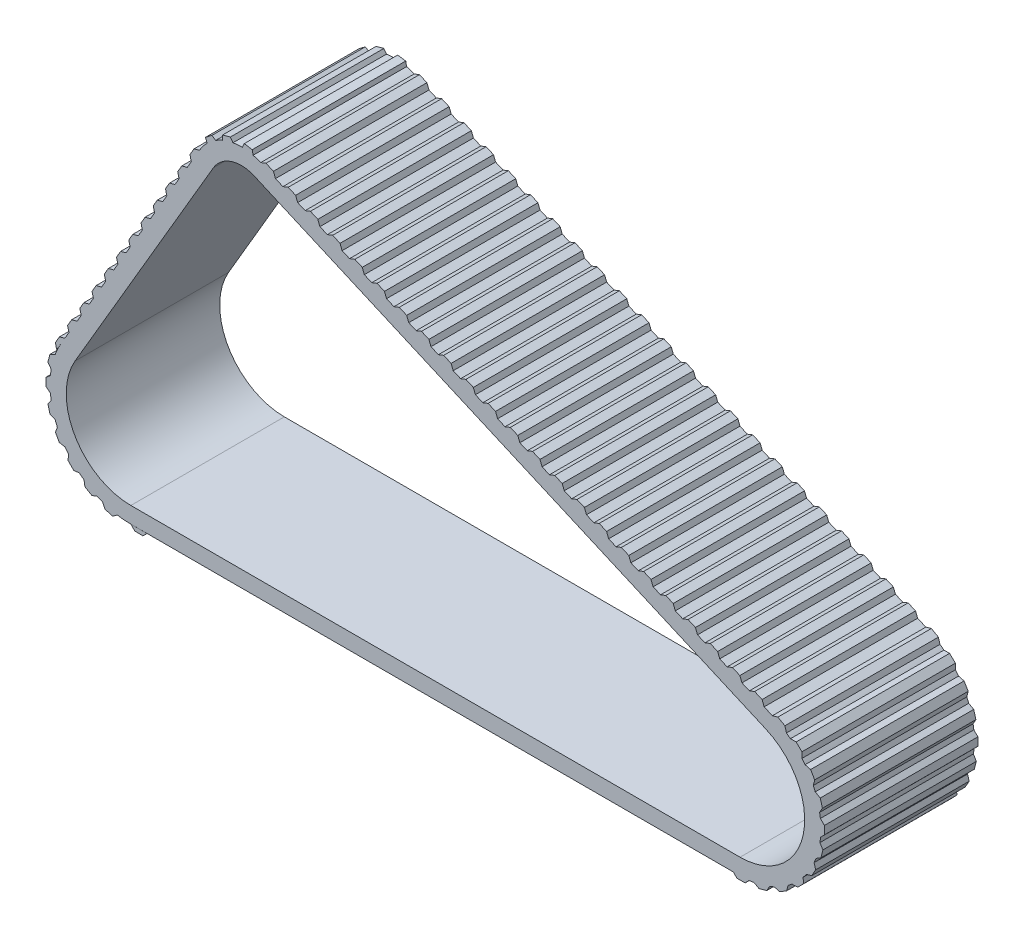
SolidWorks part; units mm, degrees
material "Caucho"
ref_plane "Alzado" through (0, 0, 0) normal (0, 0, 1) x (1, 0, 0)
ref_plane "Planta" through (0, 0, 0) normal (0, 1, 0) x (1, 0, 0)
ref_plane "Vista lateral" through (0, 0, 0) normal (1, 0, 0) x (0, 0, -1)
sketch "Croquis1" plane through (0, 0, 0) normal (0, 0, 1) x (1, 0, 0)
  line L0 (8.4952, 34.325) -> (-8.6315, 5.0496)
  line L1 (16.0728, 36.7949) -> (79.4167, 9.166)
  line L2 (0, -10) -> (75.4188, -10)
  arc A0 (-8.6315, 5.0496) -> (0, -10) centre (0, 0) ccw
  arc A1 (75.4188, -10) -> (79.4167, 9.166) centre (75.4188, 0) ccw
  arc A2 (16.0728, 36.7949) -> (8.4952, 34.325) centre (13.6741, 31.2953) ccw
extrude "Extruir1" add sketch "Croquis1" along normal blind 19
shell "Vaciado1" thickness 2
sketch "Croquis2" plane through (0, 0, 2) normal (0, 0, 1) x (1, 0, 0)
  line L0 (10.2215, 33.3151) -> (-6.9052, 4.0396)
  line L1 (0, -8) -> (75.4188, -8)
  line L2 (78.6171, 7.3328) -> (15.2732, 34.9617)
  arc A0 (15.2732, 34.9617) -> (10.2215, 33.3151) centre (13.6741, 31.2953) ccw
  arc A1 (-6.9052, 4.0396) -> (0, -8) centre (0, 0) ccw
  arc A2 (75.4188, -8) -> (78.6171, 7.3328) centre (75.4188, 0) ccw
extrude "Cortar-Extruir1" cut sketch "Croquis2" against normal blind 20
sketch "Croquis3" plane through (0, 0, 19) normal (0, 0, 1) x (1, 0, 0)
  line L0 (8.4952, 34.325) -> (7.8199, 34.1408)
  line L1 (8.4952, 34.325) -> (7.4853, 32.5987)
  line L2 (8.4952, 34.325) -> (-8.6315, 5.0496) construction
  line L3 (7.3149, 33.2777) -> (7.8199, 34.1408)
  line L4 (7.4853, 32.5987) -> (7.3149, 33.2777)
  line L5 (7.9902, 33.4618) -> (7.5674, 33.7092) construction
  dimension "D1" = 2
  dimension "D2" = 0.7
  dimension "D3" = 1
extrude "Extruir2" add sketch "Croquis3" against normal up to surface (19 mm away) up to face at (29.1763, 10.2182, 0)
sketch "Croquis5" plane through (0, 0, 19) normal (0, 0, 1) x (1, 0, 0)
  line L1 (0, -10) -> (75.4188, -10) construction
  line L2 (16.0728, 36.7949) -> (17.906, 35.9953)
  line L3 (79.4167, 9.166) -> (16.0728, 36.7949) construction
  line L4 (16.9894, 36.3951) -> (17.1893, 36.8534) construction
  line L5 (16.0728, 36.7949) -> (16.731, 37.0533)
  line L6 (16.731, 37.0533) -> (17.6476, 36.6535)
  line L7 (17.6476, 36.6535) -> (17.906, 35.9953)
  line L8 (16.0728, 36.7949) -> (79.4167, 9.166) construction
  dimension "D1" = 2
  dimension "D2" = 0.5
pattern_linear "MatrizL1" count 12 spacing 3 along (-0.505, -0.8631, 0) of "Extruir2"
extrude "Extruir3" add sketch "Croquis5" against normal up to surface (19 mm away) up to face at (29.1763, 10.2182, 0)
sketch "Croquis7" plane through (0, 0, 19) normal (0, 0, 1) x (1, 0, 0)
  line L0 (16.0728, 36.7949) -> (79.4167, 9.166) construction
pattern_linear "MatrizL2" count 23 spacing 3 along (0.9166, -0.3998, 0) of "Extruir3"
sketch "Croquis8" plane through (0, 0, 19) normal (0, 0, 1) x (1, 0, 0)
  line L1 (11.3567, 37.399) -> (11.3411, 36.8231)
  line L2 (11.3567, 37.399) -> (12.3213, 37.6627)
  line L3 (12.3213, 37.6627) -> (12.6409, 37.2056)
  arc A0 (12.6409, 37.2056) -> (11.3411, 36.8231) centre (13.6741, 31.2953) ccw
  arc A2 (16.0728, 36.7949) -> (8.4952, 34.325) centre (13.6741, 31.2953) ccw construction
extrude "Extruir4" add sketch "Croquis8" against normal up to surface (19 mm away) up to face at (29.1763, 10.2182, 0)
pattern_circular "MatrizC2" count 2 every 22 about axis through (13.6741, 31.2953, 0) along (0, 0, 1) of "Extruir4"
pattern_circular "MatrizC3" count 2 every 24 about axis through (13.6741, 31.2953, 0) along (0, 0, 1) of "Extruir4"
sketch "Croquis9" plane through (0, 0, 19) normal (0, 0, 1) x (1, 0, 0)
  line L0 (79.4167, 9.166) -> (81.1608, 8.1871)
  line L1 (80.0975, 9.3573) -> (79.4167, 9.166)
  line L2 (80.9695, 8.8679) -> (81.1608, 8.1871)
  line L3 (80.0975, 9.3573) -> (80.9695, 8.8679)
  arc A0 (75.4188, -10) -> (79.4167, 9.166) centre (75.4188, 0) ccw construction
  dimension "D1" = 2
extrude "Extruir5" add sketch "Croquis9" against normal up to surface (19 mm away) up to face at (29.1763, 10.2182, 0)
pattern_circular "MatrizC4" count 11 every 15 about axis through (75.4188, 0, 0) along (0, 0, 1) of "Extruir5"
sketch "Croquis10" plane through (0, 0, 19) normal (0, 0, 1) x (1, 0, 0)
  line L1 (0, -10) -> (2, -10.0121)
  line L2 (0, -10) -> (0.5, -10.5)
  line L3 (1.5, -10.5121) -> (2, -10.0121)
  line L4 (0.5, -10.5) -> (1.5, -10.5121)
  dimension "D1" = 2
extrude "Extruir6" add sketch "Croquis10" against normal up to surface (19 mm away) separate body up to face at (40.8036, 17.3932, 0)
sketch "Croquis12" plane through (0, 0, 0) normal (0, 0, -1) x (-1, 0, 0)
  line L0 (8.6618, -4.9974) -> (9.0948, -5.2473) construction
  line L1 (0, 0) -> (6.9396, -3.9801) construction
  line L2 (9.0948, -4.1574) -> (9.341, -4.8121)
  line L3 (9.341, -4.8121) -> (8.8486, -5.6825)
  line L4 (8.1513, -5.7928) -> (8.8486, -5.6825)
  arc A0 (0, -8) -> (6.9052, 4.0396) centre (0, 0) ccw construction
  arc A1 (8.1513, -5.7928) -> (9.0948, -4.1574) centre (0, 0) ccw
  arc A2 (0, -10) -> (8.6315, 5.0496) centre (0, 0) ccw construction
  dimension "D1" = 0.5
extrude "Extruir7" add sketch "Croquis12" against normal up to surface (19 mm away) up to face at (40.8036, 17.3932, 19)
pattern_circular "MatrizC5" count 4 every 15 about axis through (0, 0, 0) along (0, 0, 1) of "Extruir7"
pattern_circular "MatrizC6" count 4 every 15 about axis through (0, 0, 0) along (0, 0, 1) of "MatrizC5"
